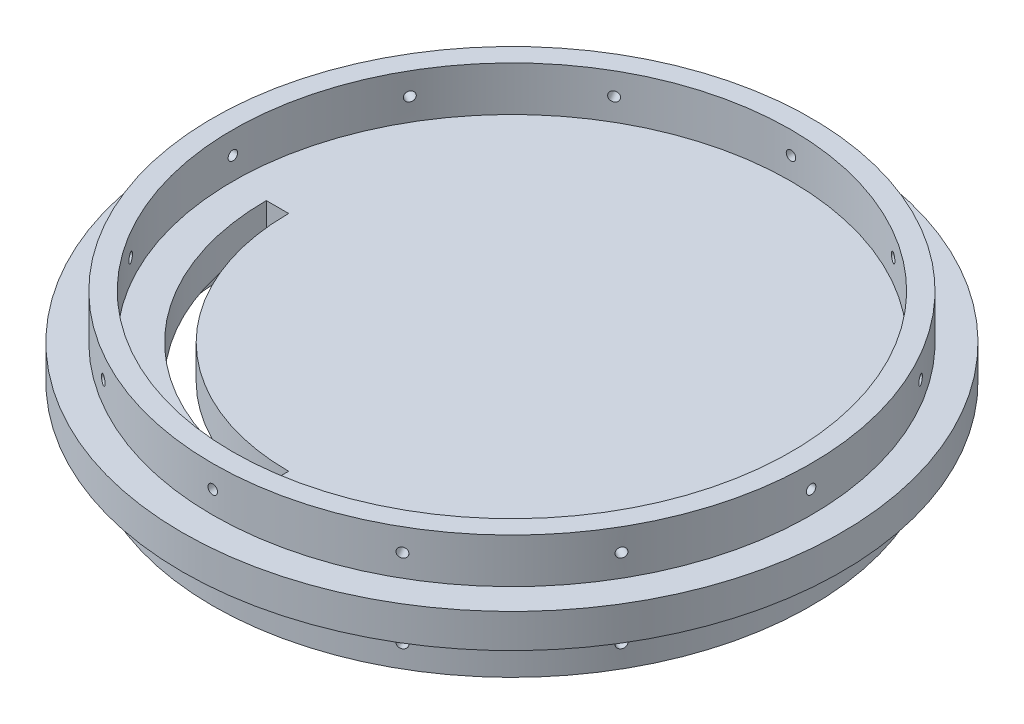
SolidWorks part; units mm, degrees
material "6061-T6 (SS)"
ref_plane "Front Plane" through (0, 0, 0) normal (0, 0, 1) x (1, 0, 0)
ref_plane "Top Plane" through (0, 0, 0) normal (0, 1, 0) x (1, 0, 0)
ref_plane "Right Plane" through (0, 0, 0) normal (1, 0, 0) x (0, 0, -1)
sketch "Sketch1" plane through (0, 0, 0) normal (0, 1, 0) x (1, 0, 0)
  circle A0 centre (0, 0) radius 93.726
  dimension "D1" = 187.452
extrude "Boss-Extrude1" add sketch "Sketch1" along normal mid plane 9.652
sketch "Sketch2" plane through (0, 0, 0) normal (0, 0, 1) x (1, 0, 0)
  line L0 (0, -18.3275) -> (0, 20.8308) construction
  line L1 (0, -4.826) -> (-19.297, -4.826)
  line L2 (-93.726, -4.826) -> (93.726, -4.826) construction
  line L3 (0, -4.826) -> (0, -1.4952)
  line L4 (-0.3818, -1.4952) -> (0, -1.4952)
  arc A0 (-19.297, -4.826) -> (-0.3818, -1.4952) centre (-0.4072, -56.7254) cw
  dimension "D6" = 55.2302
  dimension "D1" = 19.297
  dimension "D2" = 3.3308
  dimension "D3" = 0.3818
revolve "Cut-Revolve1" cut sketch "Sketch2" angle 360 about L0
sketch "Sketch4" plane through (0, 4.826, 0) normal (0, 1, 0) x (1, 0, 0)
  circle A0 centre (0, 0) radius 85.09
  circle A1 centre (0, 0) radius 79.375
  dimension "D1" = 170.18
  dimension "D2" = 158.75
extrude "Boss-Extrude2" add sketch "Sketch4" along normal blind 12.7
ref_plane "Plane1" through (0, 0, -85.09) normal (0, 0, -1) x (-1, 0, 0)
sketch "Sketch5" plane through (0, 0, -85.09) normal (0, 0, -1) x (-1, 0, 0)
  line L0 (0, 19.2786) -> (0, -19.2786) construction
  line L1 (79.375, 17.526) -> (-79.375, 17.526) construction
  circle A0 centre (0, 11.176) radius 1.3525
  dimension "D1" = 2.7051
  dimension "D2" = 6.35
extrude "Cut-Extrude2" cut sketch "Sketch5" against normal blind 12.7
pattern_circular "CirPattern1" count 12 over 360 about axis through (0, 17.526, 0) along (0, -1, 0) of "Cut-Extrude2"
mirror "Mirror2" about plane through (0, 0, 0) normal (0, 1, 0) of "CirPattern1", "Cut-Extrude2", "Boss-Extrude2"
sketch "Sketch6" plane through (0, 4.826, 0) normal (0, 1, 0) x (1, 0, 0)
  line L0 (-63.5, 0) -> (-69.85, 0)
  line L1 (0, -69.85) -> (0, -63.5)
  line L2 (0, -19.2786) -> (0, 19.2786) construction
  arc A0 (-69.85, 0) -> (0, -69.85) centre (0, 0) ccw
  arc A1 (-63.5, 0) -> (0, -63.5) centre (0, 0) ccw
  dimension "D1" = 69.85
  dimension "D2" = 63.5
  dimension "D3" = 90
extrude "Cut-Extrude3" cut sketch "Sketch6" against normal up to surface (9.652 mm away) up to face at (0, -4.826, -19.297)
